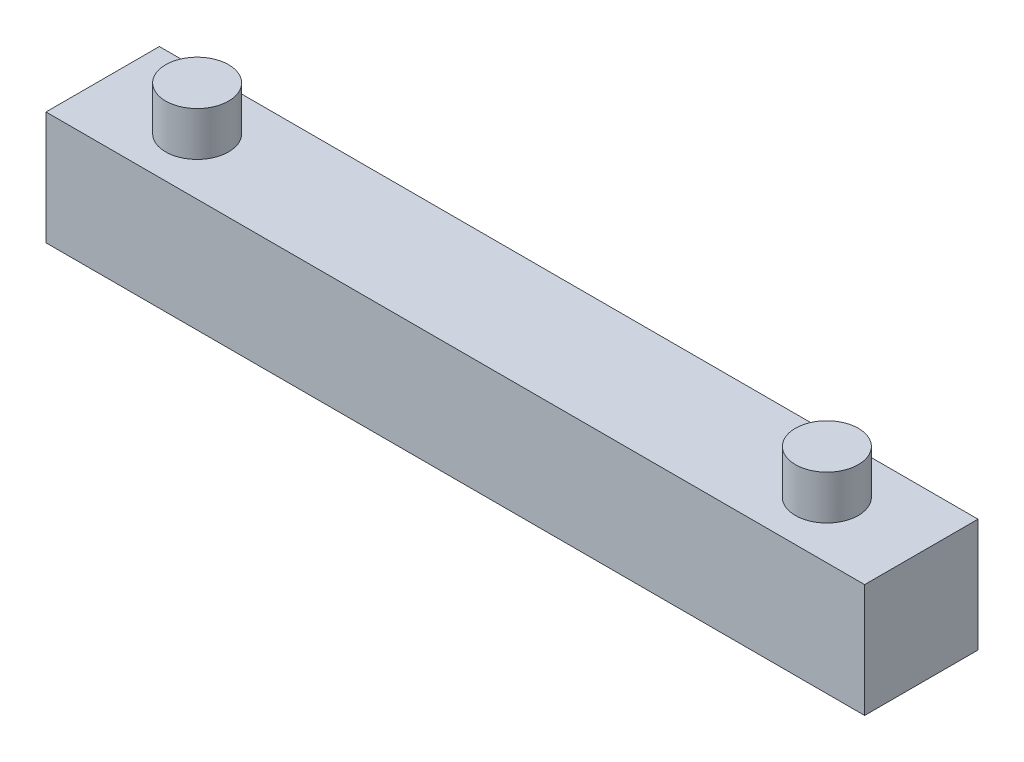
SolidWorks part; units mm, degrees
ref_plane "Front Plane" through (0, 0, 0) normal (0, 0, 1) x (1, 0, 0)
ref_plane "Top Plane" through (0, 0, 0) normal (0, 1, 0) x (1, 0, 0)
ref_plane "Right Plane" through (0, 0, 0) normal (1, 0, 0) x (0, 0, -1)
sketch "Sketch1" plane through (0, 0, 0) normal (0, 0, 1) x (1, 0, 0)
  line L0 (0, 0) -> (65, 0)
  line L1 (65, 0) -> (65, 9)
  line L2 (65, 9) -> (0, 9)
  line L3 (0, 9) -> (0, 0)
  dimension "D1" = 65
  dimension "D2" = 9
extrude "Boss-Extrude1" add sketch "Sketch1" along normal blind 9
sketch "Sketch2" plane through (0, 9, 0) normal (0, 1, 0) x (1, 0, 0)
  line L4 (65, -9) -> (0, -9) construction
  line L6 (0, -9) -> (0, 0) construction
  circle A0 centre (7.5, -4.5) radius 2.5
  circle A1 centre (57.5, -4.5) radius 2.5
  dimension "D1" = 5
  dimension "D2" = 5
  dimension "D3" = 50
  dimension "D4" = 7.5
  dimension "D6" = 4.5
extrude "Boss-Extrude2" add sketch "Sketch2" along normal blind 3.5 contours A1 | A0
